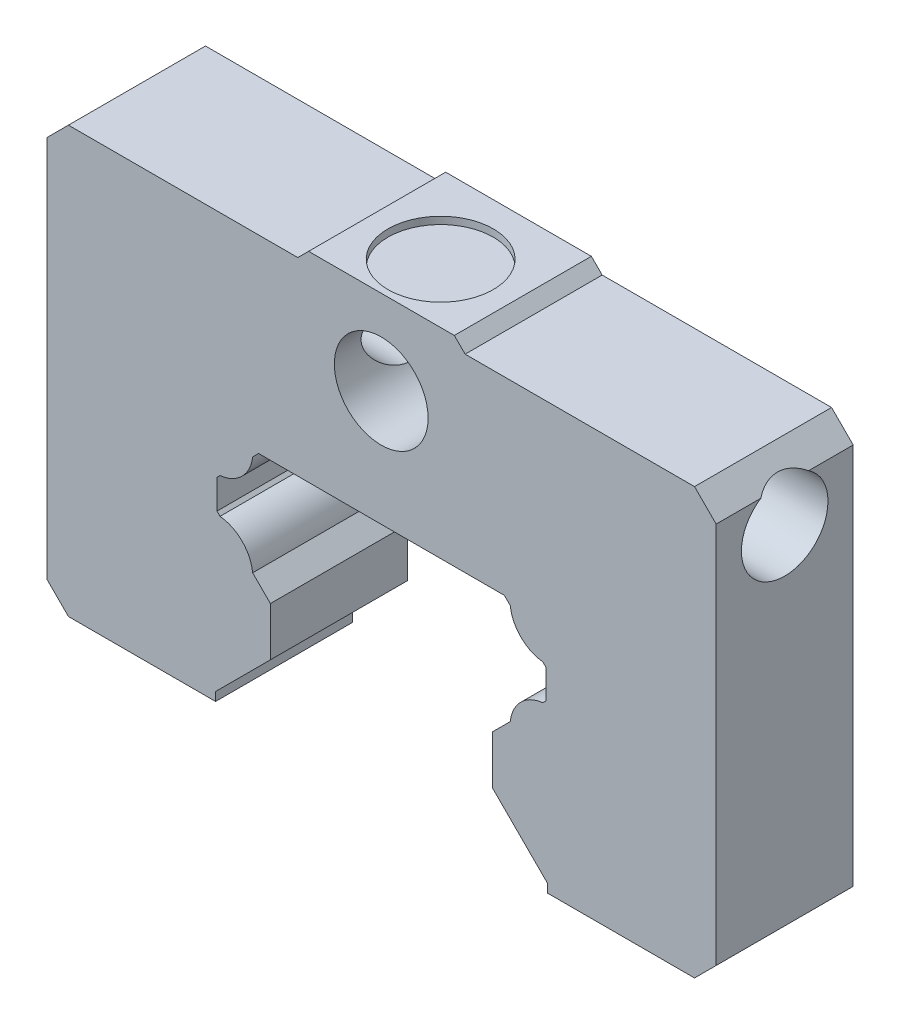
SolidWorks part; units mm, degrees
material "環氧樹脂，無填充料"
ref_plane "Front Plane" through (0, 0, 0) normal (0, 0, 1) x (1, 0, 0)
ref_plane "Top Plane" through (0, 0, 0) normal (0, 1, 0) x (1, 0, 0)
ref_plane "Right Plane" through (0, 0, 0) normal (1, 0, 0) x (0, 0, -1)
sketch "Sketch3" plane through (0, 0, 0) normal (0, 0, 1) x (1, 0, 0)
  line L0 (-21.7, 0) -> (-11.5, 0)
  line L1 (7.7, 4.4) -> (11.5, 0.6)
  line L2 (-7.7, 4.4) -> (-7.7, 7.78)
  line L3 (-7.7, 7.78) -> (-8.93, 9.01)
  line L4 (-11.4, 11.48) -> (-11.4, 13.51)
  line L5 (-11.4, 13.51) -> (-11.19, 13.7191)
  line L6 (-8.5182, 16.3791) -> (8.5182, 16.3791)
  line L7 (8.5182, 16.3791) -> (8.93, 15.9691)
  line L8 (11.4, 13.51) -> (11.4, 11.48)
  line L9 (11.4, 11.48) -> (11.19, 11.27)
  line L10 (7.7, 7.78) -> (7.7, 4.4)
  line L11 (11.5, 0.6) -> (11.5, 0)
  line L12 (11.5, 0) -> (21.7, 0)
  line L13 (-11.19, 11.27) -> (-11.4, 11.48)
  line L14 (-8.93, 15.9691) -> (-8.5182, 16.3791)
  line L15 (11.19, 13.7191) -> (11.4, 13.51)
  line L16 (8.93, 9.01) -> (7.7, 7.78)
  line L17 (-21.7, 29.5) -> (-5.8, 29.5)
  line L18 (21.7, 29.5) -> (23.2, 28)
  line L19 (23.2, 28) -> (23.2, 1.5)
  line L20 (-21.7, 29.5) -> (-23.2, 28)
  line L21 (-23.2, 28) -> (-23.2, 1.5)
  line L22 (-5.05, 30.25) -> (5.05, 30.25)
  line L23 (-23.2, 1.5) -> (-21.7, 0)
  line L24 (21.7, 0) -> (23.2, 1.5)
  line L25 (-5.8, 29.5) -> (-5.05, 30.25)
  line L26 (5.05, 30.25) -> (5.8, 29.5)
  line L27 (5.8, 29.5) -> (21.7, 29.5)
  line L29 (-7.7, 4.4) -> (-11.5, 0.6)
  line L30 (-11.5, 0.6) -> (-11.5, 0)
  arc A0 (-8.93, 9.01) -> (-11.19, 11.27) centre (-11.45, 8.75) ccw
  arc A1 (-11.19, 13.7191) -> (-8.93, 15.9691) centre (-11.45, 16.2402) ccw
  arc A2 (8.93, 15.9691) -> (11.19, 13.7191) centre (11.45, 16.2402) ccw
  arc A3 (11.19, 11.27) -> (8.93, 9.01) centre (11.45, 8.75) ccw
  dimension "D5" = 3.8
  dimension "D9" = 1.5
  dimension "D30" = 7.7
  dimension "D17" = 15.9
  dimension "D22" = 3.75
  dimension "D11" = 2.26
  dimension "D13" = 0.21
  dimension "D2" = 26.5
  dimension "D3" = 0.6
  dimension "D4" = 0.6
  dimension "D6" = 3.8
  dimension "D7" = 3.38
  dimension "D8" = 1.23
  dimension "D10" = 1.23
  dimension "D12" = 23.2
  dimension "D14" = 2.03
  dimension "D15" = 3.8
  dimension "D16" = 3.8
  dimension "D18" = 0
  dimension "D19" = 1.23
  dimension "D20" = 45
  dimension "D21" = 15.9
  dimension "D23" = 1.5
  dimension "D24" = 1.5
  dimension "D25" = 1.5
  dimension "D26" = 2.25
  dimension "D27" = 0.75
  dimension "D28" = 0.41
  dimension "D29" = 7.7
  dimension "D31" = 16.3791
  dimension "D32" = 11.4
  dimension "D33" = 1.5
extrude "Endcap 1" add sketch "Sketch3" along normal blind 9.5 separate body
hole_wizard "Tap Drill for M6x1.0 Tap1" positions "Sketch6" profile "Sketch5" hole size "M6x1.0" standard "ANSI Metric"
sketch "Sketch6" plane through (0, 0, 9.5) normal (0, 0, 1) x (1, 0, 0)
  line L2 (-8.5182, 16.3791) -> (8.5182, 16.3791) construction
  point P0 (-0.018, 24.3791)
  dimension "D1" = 8
sketch "Sketch5" plane through (-0.018, 24.3791, 9.5) normal (1, 0, 0) x (0, -1, 0)
  line L0 (0, 0) -> (0, 14.1918)
  line L1 (0, 14.1918) -> (3.25, 12.5)
  line L2 (3.25, 12.5) -> (3.25, 0)
  line L5 (3.25, 0) -> (0, 0)
  line L10 (0, 14.1918) -> (-3.25, 12.5) construction
  line L11 (0, -6.35) -> (0, 107.95) construction
  dimension "Hole Dia." = 6.5
  dimension "Hole Depth" = 12.5
  dimension "Drill Angle" = 125
hole_wizard "Tap Drill for M6x1.0 Tap2" positions "Sketch8" profile "Sketch7" hole size "M6x1.0" standard "ANSI Metric" end condition through all
sketch "Sketch8" plane through (23.2, 0, 0) normal (1, 0, 0) x (0, 0, -1)
  line L1 (-4.75, -998) -> (-4.75, 49002) construction
  line L2 (-9.5, 1.5) -> (0, 1.5) construction
  line L5 (-9.5, 29.5) -> (0, 29.5) construction
  point P0 (-4.75, 25.5)
  point P10 (-4.75, 1.5)
  dimension "D1" = 4
sketch "Sketch7" plane through (23.2, 25.5, 4.75) normal (0, 1, 0) x (0, 0, -1)
  line L0 (0, 0) -> (0, 46.4)
  line L1 (0, 46.4) -> (3, 46.4)
  line L2 (3, 46.4) -> (3, 0)
  line L5 (3, 0) -> (0, 0)
  line L11 (0, -6.35) -> (0, 107.95) construction
  dimension "Thru Hole Dia." = 6
  dimension "Thru Hole Depth" = 46.4
sketch "Sketch9" plane through (0, 30.25, 0) normal (0, 1, 0) x (1, 0, 0)
  circle A0 centre (0, -5.3994) radius 3.65
  dimension "D1" = 7.3
extrude "Cut-Extrude1" cut sketch "Sketch9" against normal blind 0.5
